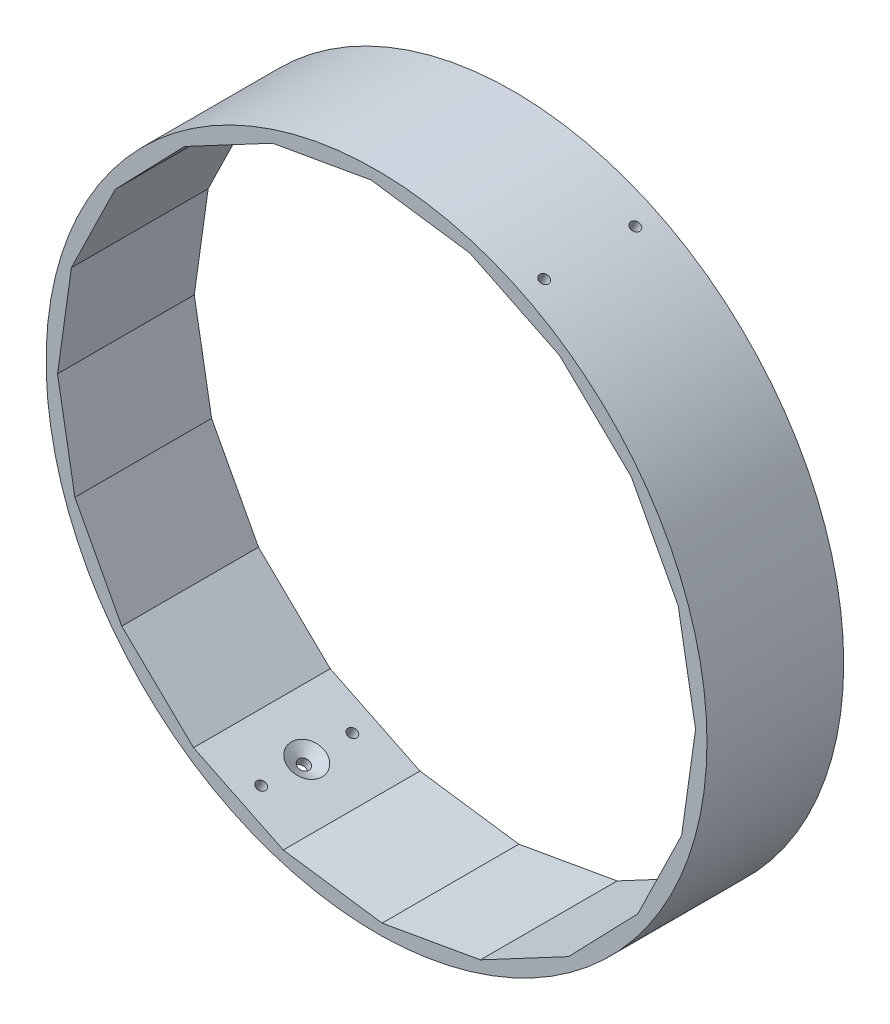
SolidWorks part; units mm, degrees
ref_plane "Ön Düzlem" through (0, 0, 0) normal (0, 0, 1) x (1, 0, 0)
ref_plane "Üst Düzlem" through (0, 0, 0) normal (0, 1, 0) x (1, 0, 0)
ref_plane "Sağ Düzlem" through (0, 0, 0) normal (1, 0, 0) x (0, 0, -1)
sketch "Çizim1" plane through (0, 0, 0) normal (0, 0, 1) x (1, 0, 0)
  line L1 (-114.6813, 80.3007) -> (-133.8827, 40.932)
  line L2 (-133.8827, 40.932) -> (-139.9787, -2.4433)
  line L3 (-139.9787, -2.4433) -> (-132.3726, -45.5795)
  line L4 (-132.3726, -45.5795) -> (-111.809, -84.2541)
  line L5 (-111.809, -84.2541) -> (-80.3007, -114.6813)
  line L6 (-80.3007, -114.6813) -> (-40.932, -133.8827)
  line L7 (-40.932, -133.8827) -> (2.4433, -139.9787)
  line L8 (2.4433, -139.9787) -> (45.5795, -132.3726)
  line L9 (45.5795, -132.3726) -> (84.2541, -111.809)
  line L10 (84.2541, -111.809) -> (114.6813, -80.3007)
  line L11 (114.6813, -80.3007) -> (133.8827, -40.932)
  line L12 (133.8827, -40.932) -> (139.9787, 2.4433)
  line L13 (139.9787, 2.4433) -> (132.3726, 45.5795)
  line L14 (132.3726, 45.5795) -> (111.809, 84.2541)
  line L15 (111.809, 84.2541) -> (80.3007, 114.6813)
  line L16 (80.3007, 114.6813) -> (40.932, 133.8827)
  line L17 (40.932, 133.8827) -> (-2.4433, 139.9787)
  line L18 (-2.4433, 139.9787) -> (-45.5795, 132.3726)
  line L19 (-45.5795, 132.3726) -> (-84.2541, 111.809)
  line L20 (-84.2541, 111.809) -> (-114.6813, 80.3007)
  circle A0 centre (0, 0) radius 145
  circle A1 centre (0, 0) radius 140 construction
extrude "Yükseklik-Ekstrüzyon1" add sketch "Çizim1" along normal blind 60
sketch "Çizim2" plane through (-60.6164, -124.282, 0) normal (0.4384, 0.8988, 0) x (0.8988, -0.4384, 0)
  circle A0 centre (0, -30) radius 2.5
extrude "Kes-Ekstrüzyon1" cut sketch "Çizim2" against normal blind 60
chamfer "Pah2" distance 5 angle 30 1 edges at (-62.8634, -123.186, 30)
sketch "Çizim3" plane through (-60.6164, -124.282, 0) normal (0.4384, 0.8988, 0) x (0.8988, -0.4384, 0)
  circle A0 centre (0, -10) radius 2.1
  circle A1 centre (0, -50) radius 2.1
extrude "Kes-Ekstrüzyon3" cut sketch "Çizim3" against normal blind 77 and the other way blind 326
